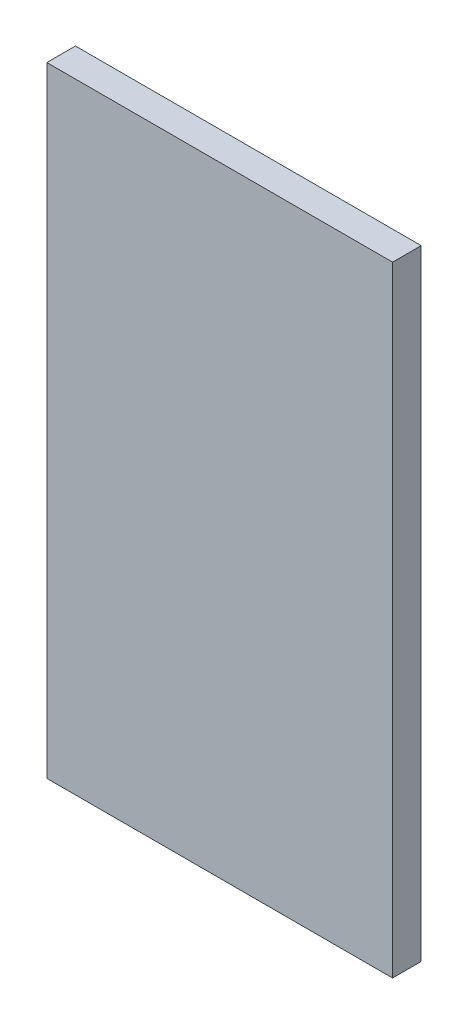
SolidWorks part; units mm, degrees
material "ABS PC"
ref_plane "Front Plane" through (0, 0, 0) normal (0, 0, 1) x (1, 0, 0)
ref_plane "Top Plane" through (0, 0, 0) normal (0, 1, 0) x (1, 0, 0)
ref_plane "Right Plane" through (0, 0, 0) normal (1, 0, 0) x (0, 0, -1)
sketch "Sketch1" plane through (0, 0, 0) normal (0, 0, 1) x (1, 0, 0)
  line L9 (-10.0659, 50.1337) -> (-19.2734, 50.1337)
  line L10 (-10.0659, 33.6237) -> (-10.0659, 50.1337)
  line L11 (-19.2734, 33.6237) -> (-10.0659, 33.6237)
  line L12 (-19.2734, 50.1337) -> (-19.2734, 33.6237)
  line L13 (-10.0659, 50.1337) -> (-19.2734, 50.1337)
  line L14 (-10.0659, 33.6237) -> (-10.0659, 50.1337)
  line L15 (-19.2734, 33.6237) -> (-10.0659, 33.6237)
  line L16 (-19.2734, 50.1337) -> (-19.2734, 33.6237)
  dimension "D1" = 0.254
extrude "Boss-Extrude1" add sketch "Sketch1" along normal blind 0.762
